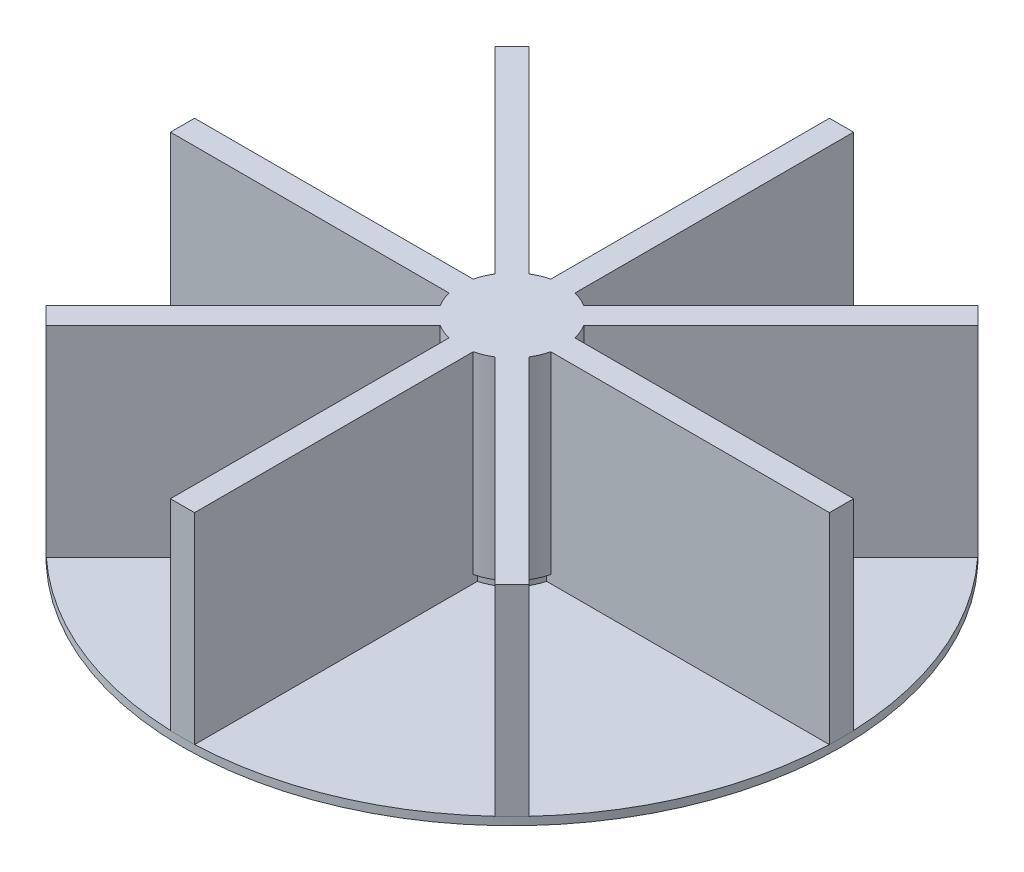
SolidWorks part; units mm, degrees
ref_plane "Front Plane" through (0, 0, 0) normal (0, 0, 1) x (1, 0, 0)
ref_plane "Top Plane" through (0, 0, 0) normal (0, 1, 0) x (1, 0, 0)
ref_plane "Right Plane" through (0, 0, 0) normal (1, 0, 0) x (0, 0, -1)
sketch "Sketch1" plane through (0, 0, 0) normal (0, 1, 0) x (1, 0, 0)
  circle A0 centre (0, 0) radius 41
  dimension "D1" = 82
extrude "Boss-Extrude1" add sketch "Sketch1" along normal blind 1
sketch "Sketch5" plane through (0, 1, 0) normal (0, 1, 0) x (1, 0, 0)
  line L0 (0, -41) -> (0, 41) construction
  line L1 (-41, 0) -> (41, 0) construction
  circle A0 centre (0, 0) radius 41 construction
sketch "Sketch6" plane through (0, 1, 0) normal (0, 1, 0) x (1, 0, 0)
  line L29 (-1.5, 0) -> (1.5, 0)
  line L30 (-1.5, 0) -> (-1.5, -41)
  line L31 (-1.5, -41) -> (1.5, -41)
  line L32 (1.5, 0) -> (1.5, -41)
  point P32 (0, 0)
  dimension "D1" = 3
  dimension "D2" = 1.5
  dimension "D3" = 41
extrude "Boss-Extrude7" add sketch "Sketch6" along normal blind 25
sketch "Sketch7" plane through (0, 0, 0) normal (0, -1, 0) x (1, 0, 0)
  circle A0 centre (0, 0) radius 6
extrude "Boss-Extrude8" add sketch "Sketch7" against normal blind 24
sketch "Sketch10" plane through (0, 0, 0) normal (0, -1, 0) x (-1, 0, 0)
  line L25 (0, 0) -> (0.2889, 53.175) construction
  line L26 (4.0389, 53.175) -> (-3.4611, 53.175) construction
  line L27 (0, 0) -> (-28.8335, 29.1484) construction
  line L29 (0, 0) -> (-15.484, 37.9637) construction
  line L30 (-3.143, 11.6778) -> (-5.9208, 10.5448)
  line L31 (-5.9208, 10.5448) -> (-7.8091, 15.1746)
  line L32 (-7.8091, 15.1746) -> (-5.0313, 16.3075)
  line L33 (-5.0313, 16.3075) -> (-3.143, 11.6778)
  circle A1 centre (0, 0) radius 41 construction
  point P29 (0, 0)
  point P58 (0, 0)
  dimension "D1" = 45
  dimension "D2" = 22.5
  dimension "D3" = 3
  dimension "D4" = 5
  dimension "D5" = 1.5
  dimension "D6" = 12
sketch "Sketch9" plane through (0, 26, 0) normal (0, 1, 0) x (1, 0, 0)
  circle A0 centre (0, 0) radius 6
extrude "Cut-Extrude3" cut sketch "Sketch9" against normal blind 5
pattern_circular "CirPattern1" count 8 over 360 about axis through (0, 0, 0) along (0, 1, 0) of "Boss-Extrude7"
sketch "Sketch11" plane through (0, 26, 0) normal (0, 1, 0) x (1, 0, 0)
  circle A0 centre (0, 0) radius 6
extrude "Cut-Extrude5" cut sketch "Sketch11" against normal blind 6
extrude "Boss-Extrude9" add sketch "Sketch10" along normal blind 2
pattern_circular "CirPattern2" count 8 over 360 about axis through (0, 0, 0) along (0, 1, 0) of "Boss-Extrude9"
fillet "Fillet1" radius 1 32 edges at (4.5319, -2, -11.1113) (6.865, -2, -12.8597) (6.4202, -2, -15.7411) (4.0871, -2, -13.9927) (11.0614, -2, -4.6524) (13.9475, -2, -4.2389) (15.6704, -2, -6.5908) (12.7844, -2, -7.0043) (11.1113, -2, 4.5319) (12.8597, -2, 6.865) (15.7411, -2, 6.4202) (13.9927, -2, 4.0871) (4.6524, -2, 11.0614) (4.2389, -2, 13.9475) (6.5908, -2, 15.6704) (7.0043, -2, 12.7844) (-4.5319, -2, 11.1113) (-6.865, -2, 12.8597) (-6.4202, -2, 15.7411) (-4.0871, -2, 13.9927) (-11.0614, -2, 4.6524) (-13.9475, -2, 4.2389) (-15.6704, -2, 6.5908) (-12.7844, -2, 7.0043) (-11.1113, -2, -4.5319) (-12.8597, -2, -6.865) (-15.7411, -2, -6.4202) (-13.9927, -2, -4.0871) (-4.6524, -2, -11.0614) (-4.2389, -2, -13.9475) (-6.5908, -2, -15.6704) (-7.0043, -2, -12.7844)
sketch "Sketch13" plane through (0, 20, 0) normal (0, 1, 0) x (1, 0, 0)
  circle A0 centre (0, 0) radius 6.5
  dimension "D1" = 13
extrude "Boss-Extrude17" add sketch "Sketch13" along normal blind 6
sketch "Sketch15" plane through (0, 0, 0) normal (0, -1, 0) x (1, 0, 0)
  circle A0 centre (0, 0) radius 6
  dimension "D1" = 12
sketch "Sketch16" plane through (0, 26, 0) normal (0, 1, 0) x (1, 0, 0)
  circle A0 centre (0, 0) radius 6.5
  circle A1 centre (0, 0) radius 6
extrude "Boss-Extrude18" add sketch "Sketch16" against normal blind 24
extrude "Boss-Extrude19" add sketch "Sketch15" along normal blind 3
sketch "Sketch17" plane through (0, -3, 0) normal (0, -1, 0) x (1, 0, 0)
  circle A0 centre (0, 0) radius 3.075
  dimension "D1" = 6.15
extrude "Cut-Extrude10" cut sketch "Sketch17" against normal blind 5
